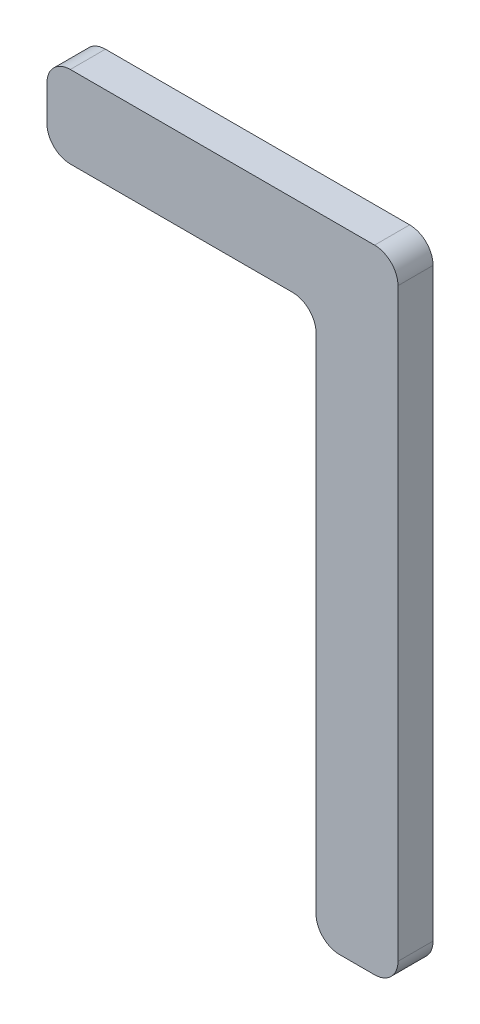
SolidWorks part; units mm, degrees
ref_plane "Front Plane" through (0, 0, 0) normal (0, 0, 1) x (1, 0, 0)
ref_plane "Top Plane" through (0, 0, 0) normal (0, 1, 0) x (1, 0, 0)
ref_plane "Right Plane" through (0, 0, 0) normal (1, 0, 0) x (0, 0, -1)
sketch "Sketch1" plane through (0, 0, 0) normal (0, 0, 1) x (1, 0, 0)
  line L0 (10, 0) -> (140, 0)
  line L1 (150, -10) -> (150, -260)
  line L2 (140, -270) -> (125, -270)
  line L3 (115, -260) -> (115, -45)
  line L4 (105, -35) -> (10, -35)
  line L5 (0, -25) -> (0, -10)
  arc A0 (115, -45) -> (105, -35) centre (105, -45) ccw
  arc A1 (140, 0) -> (150, -10) centre (140, -10) cw
  arc A2 (140, -270) -> (150, -260) centre (140, -260) ccw
  arc A3 (125, -270) -> (115, -260) centre (125, -260) cw
  arc A4 (0, -25) -> (10, -35) centre (10, -25) ccw
  arc A5 (0, -10) -> (10, 0) centre (10, -10) cw
  point P11 (150, 0)
  point P14 (150, -270)
  point P17 (115, -270)
  point P20 (0, -35)
  point P23 (0, 0)
  dimension "D5" = 10
  dimension "D6" = 10
  dimension "D7" = 10
  dimension "D1" = 150
  dimension "D2" = 270
  dimension "D3" = 35
  dimension "D4" = 35
extrude "Boss-Extrude1" add sketch "Sketch1" along normal blind 15
sketch "Sketch2" plane through (0, 0, 15) normal (0, 0, 1) x (1, 0, 0)
  line L0 (20, 0) -> (20, -35) construction
  line L1 (140, 0) -> (10, 0) construction
  line L2 (10, -35) -> (105, -35) construction
  line L3 (0, -10) -> (0, -25) construction
  line L4 (112.0711, -37.9289) -> (112.0711, 0) construction
  line L5 (112.0711, -37.9289) -> (150, -37.9289) construction
  line L6 (150, -260) -> (150, -10) construction
  line L7 (112.0711, 0) -> (150, -37.9289) construction
  arc A0 (115, -45) -> (105, -35) centre (105, -45) ccw construction
  point P8 (20, -17.5)
  point P9 (-36.6723, 1.1902)
  dimension "D1" = 20
